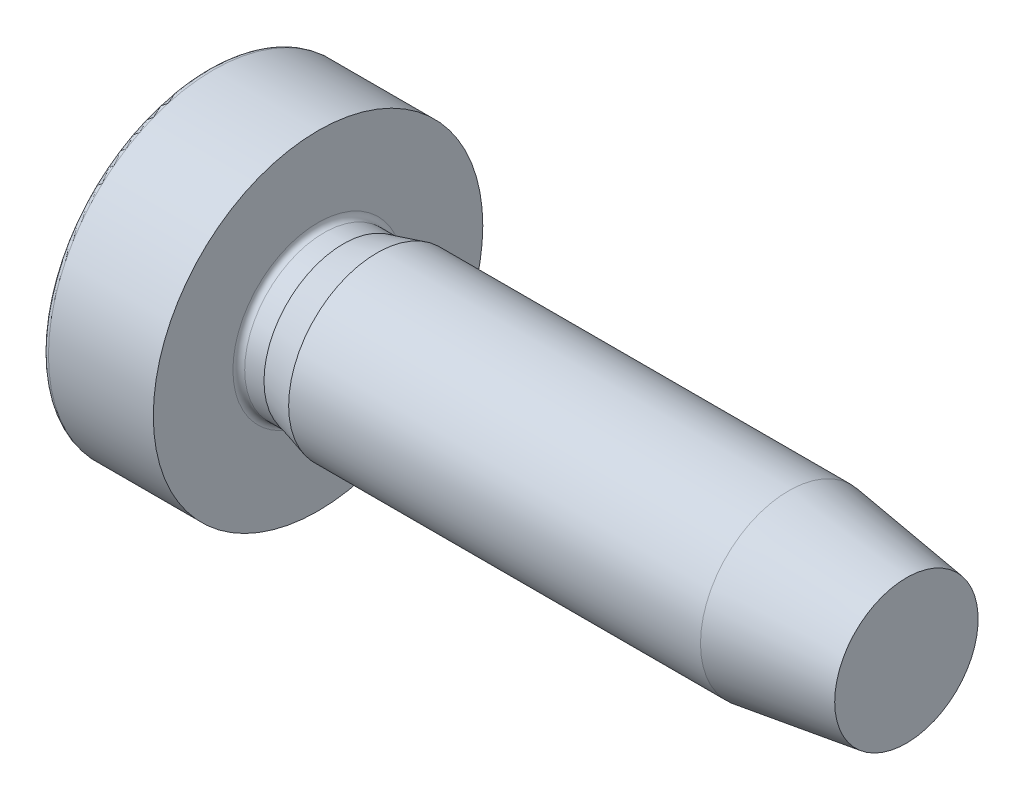
SolidWorks part; units mm, degrees
ref_plane "Front Plane" through (0, 0, 0) normal (0, 0, 1) x (1, 0, 0)
ref_plane "Top Plane" through (0, 0, 0) normal (0, 1, 0) x (1, 0, 0)
ref_plane "Right Plane" through (0, 0, 0) normal (1, 0, 0) x (0, 0, -1)
ref_plane "Plane1" through (0, 0, 0) normal (0, 0, 1) x (1, 0, 0)
sketch "Sketch1" plane through (0, 0, 0) normal (0, 0, 1) x (1, 0, 0)
  line L0 (-1.7823, 2.8) -> (0, 2.8)
  line L1 (0, 2.8) -> (0, 1.4467)
  line L2 (0.1, 1.3468) -> (0.4281, 1.3468)
  line L3 (0.4281, 1.3468) -> (1, 1.5)
  line L4 (1, 1.5) -> (8, 1.5)
  line L5 (8, 1.5) -> (10, 1.2189)
  line L6 (10, 1.2189) -> (10, 0)
  line L7 (10, 0) -> (-2.4, 0)
  line L8 (13, 0) -> (-5.4, 0) construction
  arc A0 (-2.4, 0) -> (-1.8752, 2.737) centre (5, 0) cw
  arc A1 (-1.8752, 2.737) -> (-1.7823, 2.8) centre (-1.7823, 2.7) cw
  arc A2 (0, 1.4467) -> (0.1, 1.3468) centre (0.1, 1.4467) ccw
revolve "Revolve1" add sketch "Sketch1" angle 360 about L8
ref_plane "Plane2" through (-2.4, 0, 0) normal (1, 0, 0) x (0, 0, -1)
sketch "Sketch2" plane through (-2.4, 0, 0) normal (1, 0, 0) x (0, 0, -1)
  line L0 (-1.5, 0.375) -> (-1.5, -0.375)
  line L1 (-1.5, -0.375) -> (-0.6, -0.2963)
  line L2 (-0.6, -0.2963) -> (-0.375, -0.375)
  line L3 (-0.375, -0.375) -> (-0.2963, -0.6)
  line L4 (-0.2963, -0.6) -> (-0.375, -1.5)
  line L5 (-0.375, -1.5) -> (0.375, -1.5)
  line L6 (0.375, -1.5) -> (0.2963, -0.6)
  line L7 (0.2963, -0.6) -> (0.375, -0.375)
  line L8 (0.375, -0.375) -> (0.6, -0.2963)
  line L9 (0.6, -0.2963) -> (1.5, -0.375)
  line L10 (1.5, -0.375) -> (1.5, 0.375)
  line L11 (1.5, 0.375) -> (0.6, 0.2963)
  line L12 (0.6, 0.2963) -> (0.375, 0.375)
  line L13 (0.375, 0.375) -> (0.2963, 0.6)
  line L14 (0.2963, 0.6) -> (0.375, 1.5)
  line L15 (0.375, 1.5) -> (-0.375, 1.5)
  line L16 (-0.375, 1.5) -> (-0.2963, 0.6)
  line L17 (-0.2963, 0.6) -> (-0.375, 0.375)
  line L18 (-0.375, 0.375) -> (-0.6, 0.2963)
  line L19 (-0.6, 0.2963) -> (-1.5, 0.375)
extrude "Cut-Extrude1" cut sketch "Sketch2" against normal blind 1.2 and the other way blind 1.2
